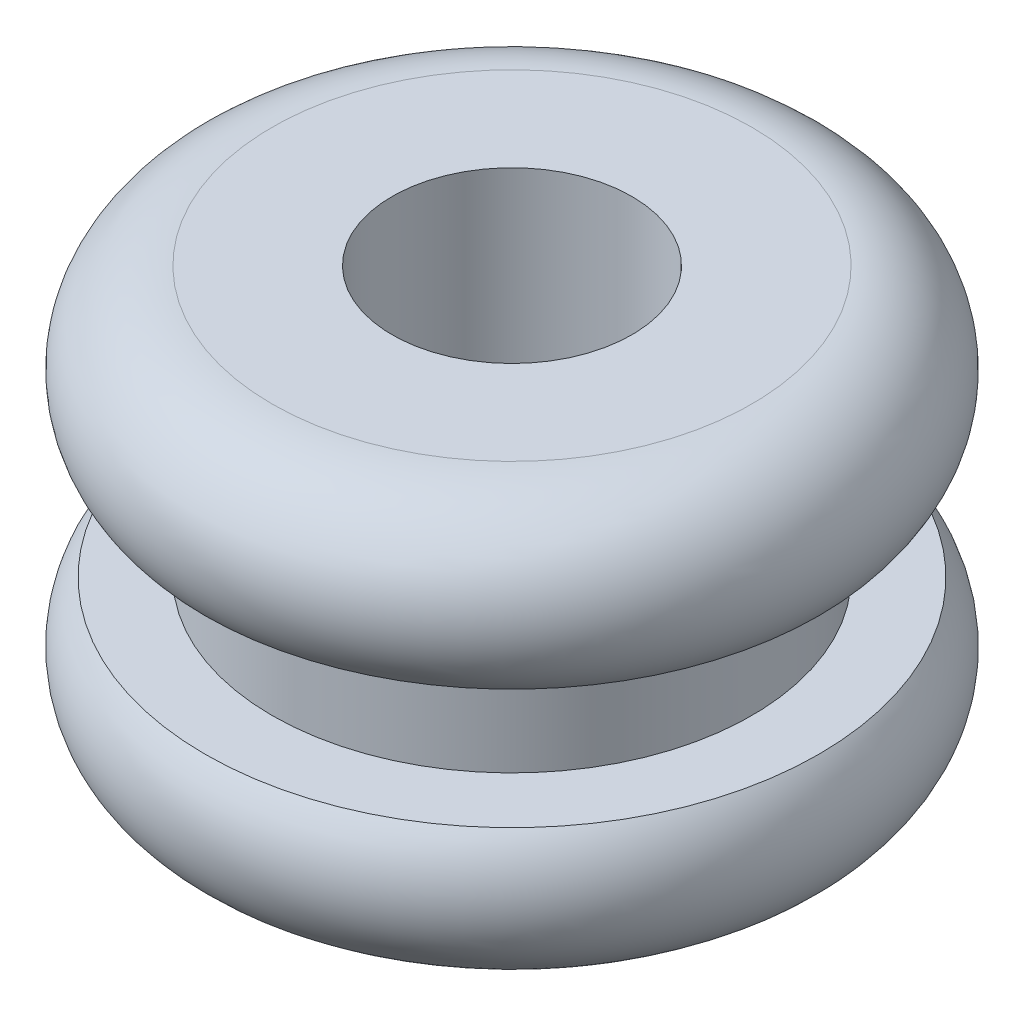
SolidWorks part; units mm, degrees
ref_plane "Front" through (0, 0, 0) normal (0, 0, 1) x (1, 0, 0)
ref_plane "Top" through (0, 0, 0) normal (0, 1, 0) x (1, 0, 0)
ref_plane "Right" through (0, 0, 0) normal (1, 0, 0) x (0, 0, -1)
sketch "Sketch1" plane through (0, 0, 0) normal (1, 0, 0) x (0, 0, -1)
  line L0 (0, -2.7781) -> (0, 2.7781) construction
  line L1 (0, 0.7937) -> (0, -0.7937) construction
  line L2 (-4.3656, 2.7781) -> (4.3656, 2.7781) construction
  line L3 (-1.5875, 0.7937) -> (1.5875, 0.7938) construction
  line L4 (-3.175, 0) -> (3.175, 0) construction
  point P12 (-1.5875, 0.7937)
  point P13 (1.5875, 0.7938)
  point P14 (-3.175, 0)
  point P15 (3.175, 0)
  point P16 (-4.3656, 2.7781)
  point P17 (0, -2.7781)
  point P18 (4.3656, 2.7781)
  point P19 (0, 2.7781)
  point P20 (0, 0.7937)
  point P21 (0, -0.7937)
  dimension "Overall Height E" = 5.5562
  dimension "Material Thickness B" = 1.5875
  dimension "Flange Diameter D" = 8.7312
  dimension "ID C" = 3.175
  dimension "For ID A" = 6.35
sketch "Sketch2" plane through (0, 0, 0) normal (1, 0, 0) x (0, 0, -1)
  line L0 (-1.5875, -2.7781) -> (-1.5875, 2.7781)
  line L1 (-1.5875, 2.7781) -> (-3.175, 2.7781)
  line L2 (-3.175, 0.7937) -> (-3.175, -0.7937)
  line L3 (-3.175, 0.7937) -> (-4.0624, 0.7937)
  line L4 (-3.175, -0.7937) -> (-4.0624, -0.7937)
  line L5 (-1.5875, -2.7781) -> (-3.175, -2.7781)
  arc A0 (-4.0624, 0.7937) -> (-3.175, 2.7781) centre (-3.175, 1.5875) cw
  arc A1 (-4.0624, -0.7937) -> (-3.175, -2.7781) centre (-3.175, -1.5875) ccw
  point P4 (-4.3656, 1.5875)
revolve "Revolve1" add sketch "Sketch2" angle 360 about L0
ref_plane "Plane1" through (0, 2.7781, 0) normal (0, -1, 0) x (0, 0, -1)
sketch "Sketch3" plane through (0, 2.7781, 0) normal (0, -1, 0) x (0, 0, -1)
  line L0 (0, -4.3656) -> (0, 4.3656) construction
  line L1 (-4.3656, 0) -> (4.3656, 0) construction
  line L2 (0, 1.5875) -> (0, -1.5875) construction
  line L3 (-1.5875, 0) -> (1.5875, 0) construction
  line L4 (0, 3.175) -> (0, -3.175) construction
  line L5 (-3.175, 0) -> (3.175, 0) construction
  point P11 (0, 4.3656)
  point P12 (0, 1.5875)
  point P13 (0, -1.5875)
  point P14 (0, -4.3656)
  point P19 (0, -3.175)
  point P20 (0, 3.175)
